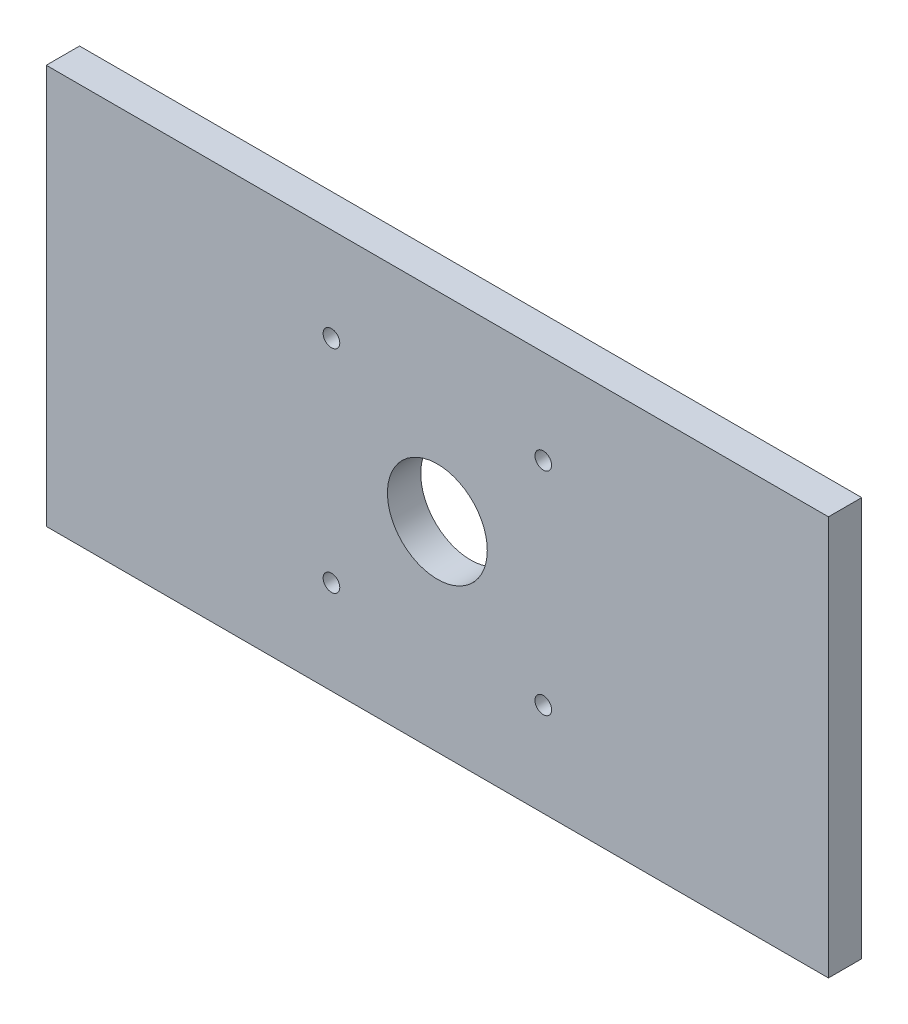
SolidWorks part; units mm, degrees
ref_plane "Front Plane" through (0, 0, 0) normal (0, 0, 1) x (1, 0, 0)
ref_plane "Top Plane" through (0, 0, 0) normal (0, 1, 0) x (1, 0, 0)
ref_plane "Right Plane" through (0, 0, 0) normal (1, 0, 0) x (0, 0, -1)
sketch "Sketch1" plane through (0, 0, 0) normal (0, 0, 1) x (1, 0, 0)
  line L1 (-117.5, -60) -> (117.5, -60)
  line L2 (-117.5, -60) -> (-117.5, 60)
  line L3 (-117.5, 60) -> (117.5, 60)
  line L4 (117.5, -60) -> (117.5, 60)
  line L5 (-117.5, -60) -> (117.5, 60) construction
  line L6 (-117.5, 60) -> (117.5, -60) construction
  point P0 (0, 0)
  dimension "D1" = 235
  dimension "D2" = 120
extrude "Boss-Extrude1" add sketch "Sketch1" along normal blind 10
sketch "Sketch2" plane through (0, 0, 10) normal (0, 0, 1) x (1, 0, 0)
  circle A0 centre (0, 0) radius 15
  dimension "D1" = 30
extrude "Cut-Extrude1" cut sketch "Sketch2" against normal blind 10
sketch "Sketch3" plane through (0, 0, 10) normal (0, 0, 1) x (1, 0, 0)
  circle A2 centre (31.8198, 31.8198) radius 2.5
  circle A4 centre (31.8198, -31.8198) radius 2.5
  circle A6 centre (-31.8198, -31.8198) radius 2.5
  circle A8 centre (-31.8198, 31.8198) radius 2.5
  point P21 (0, 0)
  dimension "D1" = 63.6396
  dimension "D3" = 5
  dimension "D2" = 63.6396
extrude "Cut-Extrude2" cut sketch "Sketch3" against normal blind 10
